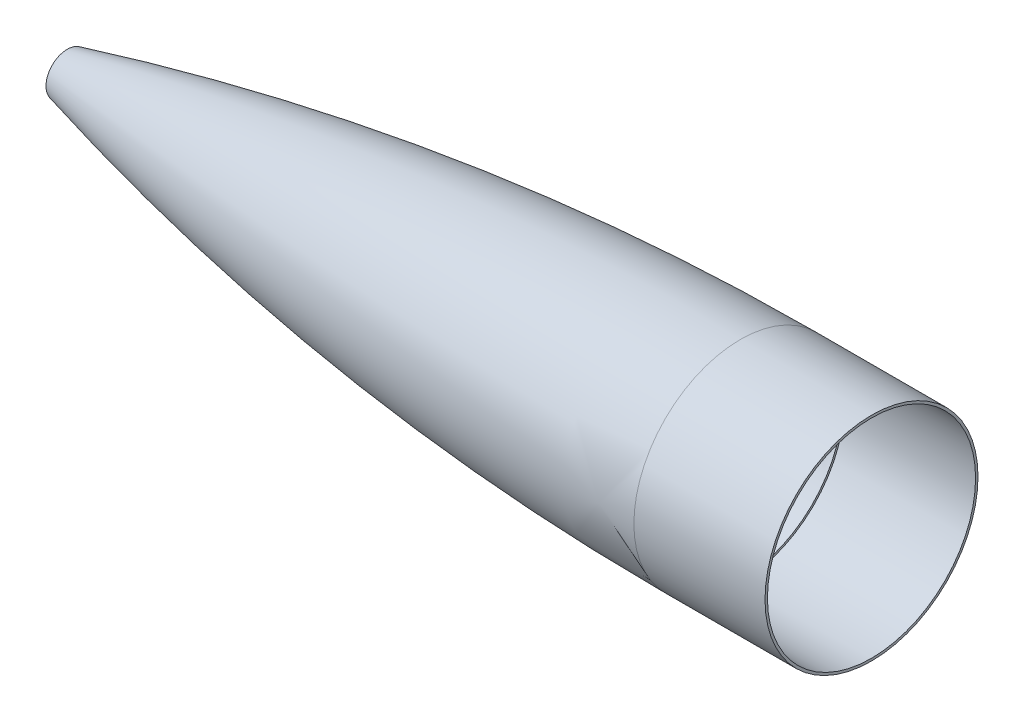
SolidWorks part; units mm, degrees
other "Nose Cone Body" parameters "D1"=838.2, "D2"=28.9967, "D3"=74.178, "D4"=112.7691
material "E-Glass Fiber"
ref_plane "Front Plane" through (0, 0, 0) normal (0, 0, 1) x (1, 0, 0)
ref_plane "Top Plane" through (0, 0, 0) normal (0, 1, 0) x (1, 0, 0)
ref_plane "Right Plane" through (0, 0, 0) normal (1, 0, 0) x (0, 0, -1)
sketch "Ogive Sketch" plane through (0, 0, 0) normal (0, 0, 1) x (1, 0, 0)
  line L2 (0, 0) -> (654.05, 0) construction
  line L3 (654.05, 0) -> (654.05, 78.359)
  line L4 (0, 0) -> (654.05, 0)
  line L5 (57.15, 0) -> (57.15, 15.6253)
  line L7 (552.45, 78.359) -> (654.05, 78.359)
  arc A1 (552.45, 78.359) -> (0, 0) centre (552.45, -1908.2739) ccw
  dimension "D1" = 78.359
  dimension "D3" = 57.15
  dimension "D2" = 654.05
  dimension "D4" = 101.6
revolve "Ogive Body Revolve" add sketch "Ogive Sketch" angle 360 about L4
shell "Ogive Shell" thickness 3.302
sketch "Sketch7" plane through (654.05, 0, 0) normal (1, 0, 0) x (0, 0, -1)
  circle A0 centre (0, 0) radius 76.581
  circle A1 centre (0, 0) radius 78.359 construction
  dimension "D1" = 1.778
extrude "Cut-Extrude8" cut sketch "Sketch7" against normal blind 101.6
sketch "Sketch3" plane through (0, 0, 0) normal (0, 1, 0) x (1, 0, 0)
  line L1 (654.05, 78.359) -> (648.9375, 78.359)
  line L2 (654.05, 78.359) -> (654.05, -78.359)
  line L3 (654.05, -78.359) -> (648.9375, -78.359)
  line L4 (648.9375, 78.359) -> (648.9375, -78.359)
  line L5 (654.05, -78.359) -> (654.05, 78.359) construction
  point P6 (0, 0)
  point P7 (654.05, 78.359)
  point P8 (648.9375, 81.5884)
  point P9 (654.05, 64.9087)
  point P11 (0, 0)
  dimension "D1" = 5.1125
  dimension "D2" = 78.359
  dimension "D3" = 78.359
extrude "Cut-Extrude5" cut sketch "Sketch3" against normal through all both and the other way through all
equation "\"L\"=25.75"
equation "\"OD\"= 6.17"
equation "\"R\"= \"OD\" / 2"
equation "\"C\"= 0 / 3"
equation "\"rho\"= ( \"R\" ^ 2 + \"L\" ^ 2 ) / ( 2 * \"R\" )"
equation "\"ID\"= 6"
equation "\"Tip Length\"= 2.25"
equation "\"D3@Ogive Sketch\" = \"Tip Length\""
equation "\"D1@Ogive Sketch\"=\"OD\" / 2"
equation "\"Coupler_Dia\"= 6"
equation "\"Coupler_Length\"= 4"
equation "\"D2@Ogive Sketch\"=\"L\""
equation "\"D2@Sketch3\"=\"OD\"/2"
equation "\"D3@Sketch3\"=\"OD\"/2"
